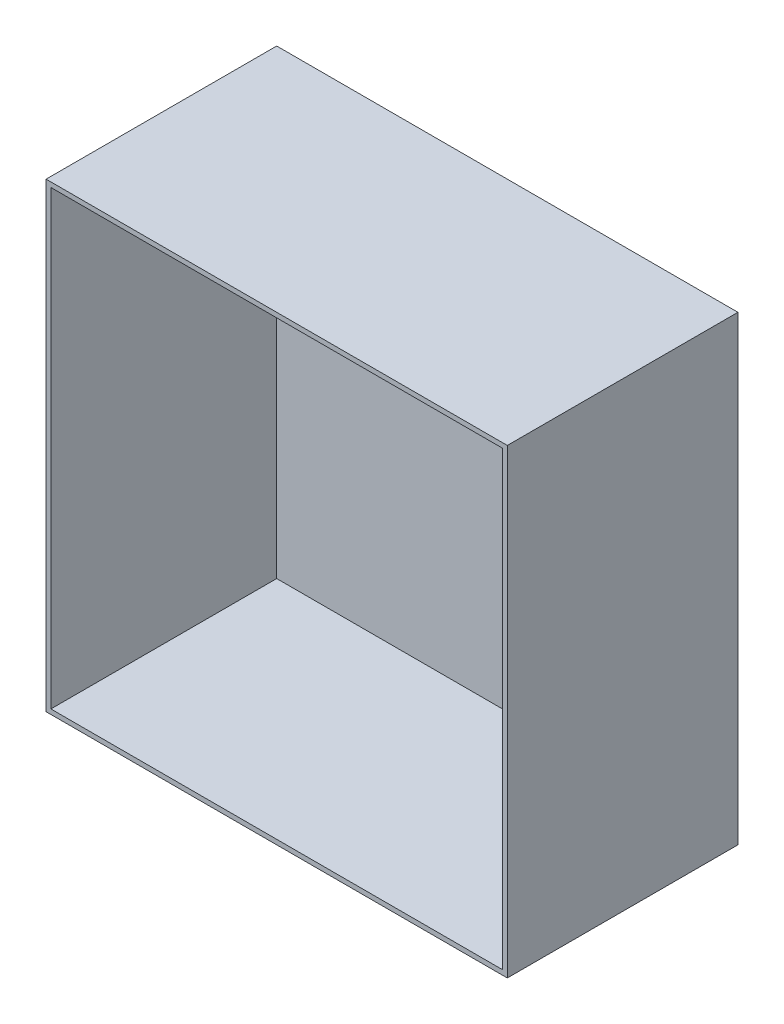
SolidWorks part; units mm, degrees
material "1060 Alloy"
ref_plane "Front Plane" through (0, 0, 0) normal (0, 0, 1) x (1, 0, 0)
ref_plane "Top Plane" through (0, 0, 0) normal (0, 1, 0) x (1, 0, 0)
ref_plane "Right Plane" through (0, 0, 0) normal (1, 0, 0) x (0, 0, -1)
sketch "Sketch1" plane through (0, 0, 0) normal (0, 0, 1) x (1, 0, 0)
  line L1 (0, 0) -> (152.4, 0)
  line L2 (0, 0) -> (0, 152.4)
  line L3 (0, 152.4) -> (152.4, 152.4)
  line L4 (152.4, 0) -> (152.4, 152.4)
  dimension "D1" = 152.4
  dimension "D2" = 152.4
extrude "Boss-Extrude1" add sketch "Sketch1" along normal blind 76.2
shell "Shell1" thickness 1.5875
